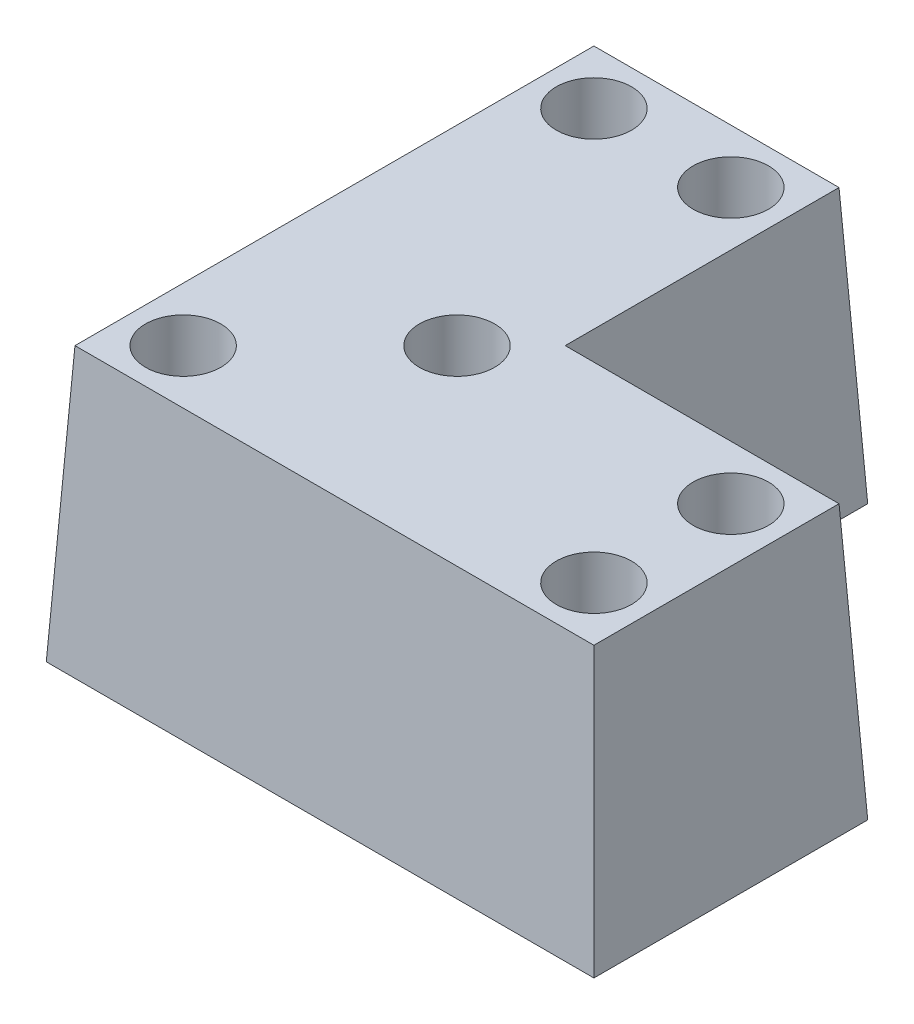
SolidWorks part; units mm, degrees
ref_plane "Front Plane" through (0, 0, 0) normal (0, 0, 1) x (1, 0, 0)
ref_plane "Top Plane" through (0, 0, 0) normal (0, 1, 0) x (1, 0, 0)
ref_plane "Right Plane" through (0, 0, 0) normal (1, 0, 0) x (0, 0, -1)
sketch "Sketch1" plane through (0, 0, 0) normal (0, 1, 0) x (1, 0, 0)
  line L0 (10, 86.2592) -> (10, -24.6455) construction
  line L1 (0, 0) -> (80, 0)
  line L2 (0, 0) -> (0, 80)
  line L3 (0, 80) -> (40, 80)
  line L4 (80, 0) -> (80, 40)
  line L7 (80, 40) -> (40, 40)
  line L8 (40, 80) -> (40, 40)
  line L9 (30, 90.3667) -> (30, -27.7751) construction
  line L10 (92.5183, 30) -> (-23.4719, 30) construction
  line L11 (92.5183, 10) -> (-23.4719, 10) construction
  line L12 (-23.4719, 50) -> (50.5621, 50) construction
  line L13 (-23.4719, 70) -> (50.5621, 70) construction
  line L14 (70, 46.9749) -> (70, -4.9519) construction
  line L15 (50, 46.9749) -> (50, -4.9519) construction
  dimension "D1" = 80
  dimension "D2" = 80
  dimension "D3" = 40
  dimension "D4" = 40
  dimension "D5" = 10
  dimension "D6" = 20
  dimension "D7" = 10
  dimension "D8" = 20
  dimension "D9" = 10
  dimension "D10" = 20
  dimension "D11" = 10
  dimension "D12" = 20
extrude "Boss-Extrude1" add sketch "Sketch1" along normal blind 40 draft 3
hole_wizard "CBORE for M5 SBHCS1" positions "Sketch2" profile "Sketch4" counterbore size "M5" standard "ANSI Metric" end condition through all
sketch "Sketch2" plane through (0, 40, 0) normal (0, 1, 0) x (1, 0, 0)
  line L0 (10, 86.2592) -> (10, -24.6455) construction
  line L1 (-23.4719, 70) -> (50.5621, 70) construction
  line L2 (30, 90.3667) -> (30, -27.7751) construction
  line L3 (92.5183, 30) -> (-23.4719, 30) construction
  line L4 (70, 46.9749) -> (70, -4.9519) construction
  line L5 (92.5183, 10) -> (-23.4719, 10) construction
  point P0 (10, 70)
  point P6 (30, 70)
  point P10 (70, 30)
  point P16 (70, 10)
  point P20 (30, 30)
  point P22 (10, 10)
sketch "Sketch4" plane through (10, 40, -70) normal (1, 0, 0) x (0, 0, 1)
  line L0 (0, 0) -> (0, 40)
  line L1 (0, 40) -> (2.75, 40)
  line L3 (2.75, 40) -> (2.75, 35)
  line L4 (2.75, 35) -> (5.5, 35)
  line L5 (5.5, 35) -> (5.5, 0)
  line L7 (5.5, 0) -> (0, 0)
  line L11 (0, -6.35) -> (0, 107.95) construction
  dimension "Thru Hole Dia." = 5.5
  dimension "Thru Hole Depth" = 40
  dimension "C'Bore Dia." = 11
  dimension "C'Bore Depth" = 35
move or copy body "Body-Move/Copy1" [suppressed] bodies to move or copy 102
